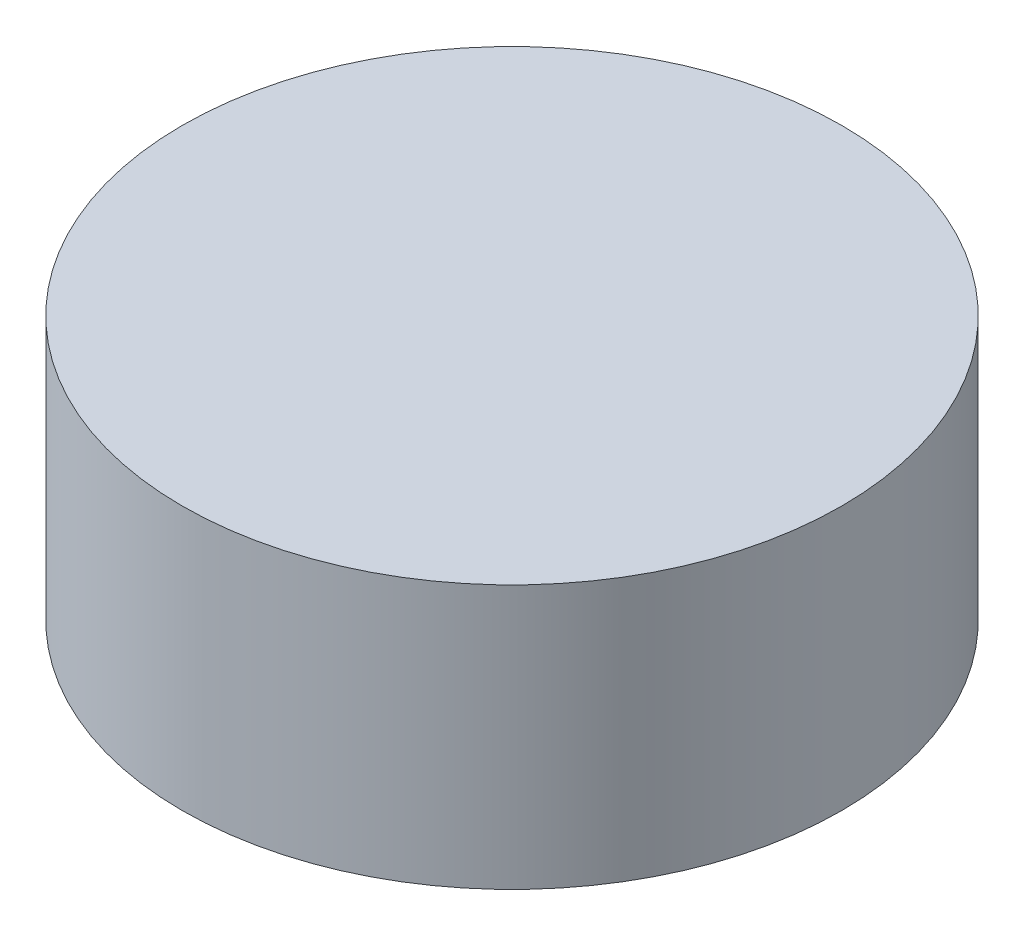
SolidWorks part; units mm, degrees
ref_plane "Alzado" through (0, 0, 0) normal (0, 0, 1) x (1, 0, 0)
ref_plane "Planta" through (0, 0, 0) normal (0, 1, 0) x (1, 0, 0)
ref_plane "Vista lateral" through (0, 0, 0) normal (1, 0, 0) x (0, 0, -1)
sketch "Croquis1" plane through (0, 0, 0) normal (0, 1, 0) x (1, 0, 0)
  circle A0 centre (0, 0) radius 1.25
  dimension "D1" = 2.5
extrude "Saliente-Extruir1" add sketch "Croquis1" along normal blind 1
